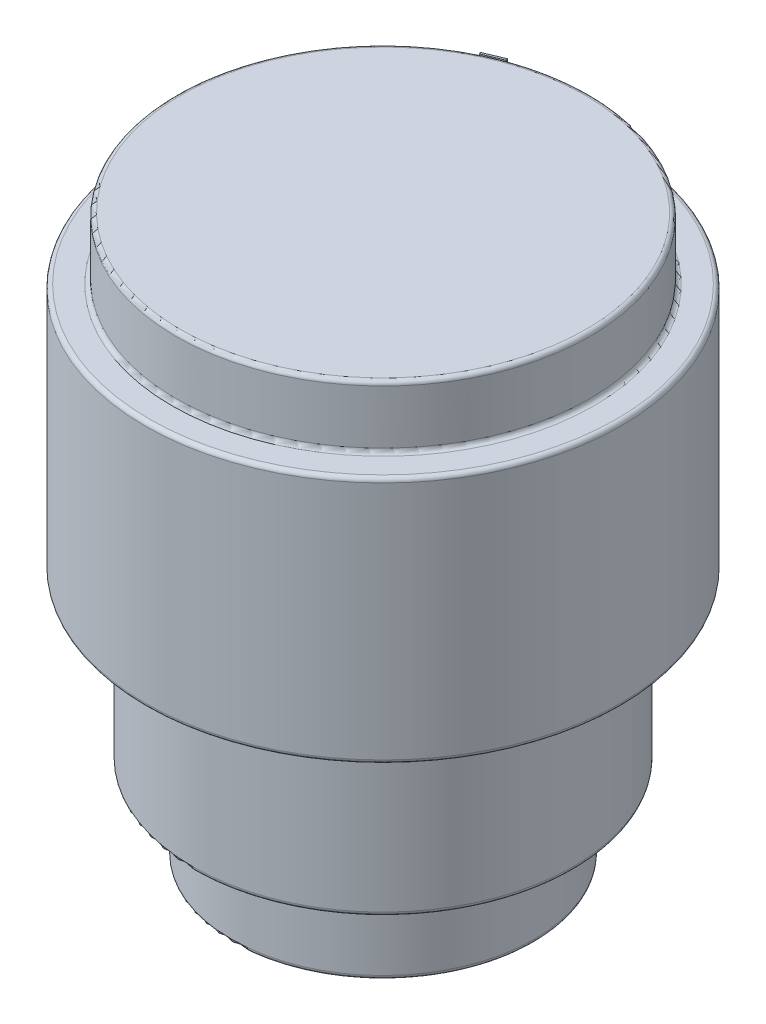
SolidWorks part; units mm, degrees
material "ABS"
ref_plane "Front Plane" through (0, 0, 0) normal (0, 0, 1) x (1, 0, 0)
ref_plane "Top Plane" through (0, 0, 0) normal (0, 1, 0) x (1, 0, 0)
ref_plane "Right Plane" through (0, 0, 0) normal (1, 0, 0) x (0, 0, -1)
sketch "Sketch1" plane through (0, 0, 0) normal (0, 0, 1) x (1, 0, 0)
  line L0 (0, 46.497) -> (0, -68.503) construction
  line L1 (0, 46.497) -> (40, 46.497) construction
  line L2 (0, 46.497) -> (25, 46.497) construction
  line L3 (0, -48.503) -> (26.5, -48.503) construction
  line L4 (0, -8.503) -> (36, -8.503) construction
  line L5 (0, 22.1791) -> (47.5, 22.1791) construction
  line L6 (0, 31.497) -> (40, 31.497) construction
  point P14 (0, 0)
  point P15 (0, 0)
  dimension "D1" = 115
  dimension "D2" = 40
  dimension "D3" = 26.5
  dimension "D4" = 36
  dimension "D5" = 47.5
  dimension "D6" = 15
  dimension "D7" = 40
  dimension "D8" = 40
sketch "Sketch2" plane through (0, 0, 0) normal (0, 0, 1) x (1, 0, 0)
  line L0 (0, -68.503) -> (26.5, -68.503)
  line L1 (26.5, -68.503) -> (26.5, -48.503)
  line L2 (26.5, -48.503) -> (36, -48.503)
  line L3 (36, -48.503) -> (36, -8.503)
  line L4 (36, -8.503) -> (47.5, -8.503)
  line L5 (47.5, -8.503) -> (47.5, 22.1791)
  line L6 (47.5, 22.1791) -> (47.5, 31.497)
  line L7 (47.5, 31.497) -> (40, 31.497)
  line L8 (40, 31.497) -> (40, 46.497)
  line L9 (40, 46.497) -> (0, 46.497)
revolve "Revolve-Thin2" add sketch "Sketch2" angle 360 about L0
fillet "Fillet1" radius 1 7 edges at (-46, -18.503, 0) (-36.5, -78.503, 0) (-46, -58.503, 0) (-57.5, -18.503, 0) (-57.5, 41.497, 0) (-50, 41.497, 0) (-50, 56.497, 0)
sketch "Sketch3" plane through (0, 56.497, 0) normal (0, 1, 0) x (1, 0, 0)
  text T0 "nikkor AF-S 20mm 1_8G ED" font "Arial Rounded MT Bold" height in points 28
extrude "Boss-Extrude1" add sketch "Sketch3" against normal offset from surface (2 mm away) 2 up to face at (49, 56.497, 0)
equation "\"D5@Sketch1\"=95/2"
equation "\"D4@Sketch1\"=72/2"
equation "\"D3@Sketch1\"=53/2"
